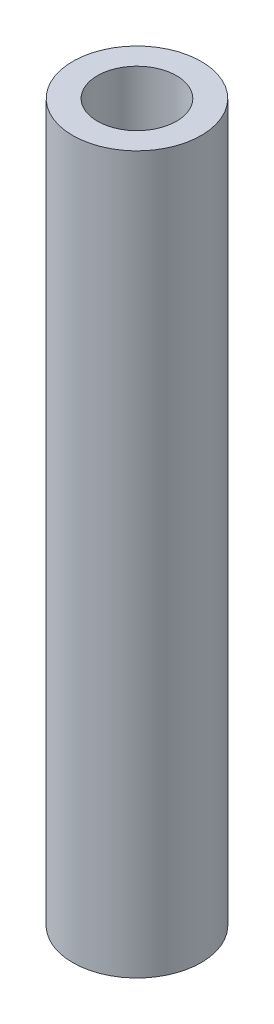
SolidWorks part; units mm, degrees
material "6061-T4 (SS)"
ref_plane "Front Plane" through (0, 0, 0) normal (0, 0, 1) x (1, 0, 0)
ref_plane "Top Plane" through (0, 0, 0) normal (0, 1, 0) x (1, 0, 0)
ref_plane "Right Plane" through (0, 0, 0) normal (1, 0, 0) x (0, 0, -1)
sketch "Sketch1" plane through (0, 0, 0) normal (0, 1, 0) x (1, 0, 0)
  line L0 (0, 0) -> (1.6, 0) construction
  line L1 (1.6, 0) -> (2.6, 0) construction
  circle A0 centre (0, 0) radius 1.6
  circle A1 centre (0, 0) radius 2.6
  dimension "D1" = 3.2
  dimension "D2" = 1
extrude "Boss-Extrude1" add sketch "Sketch1" along normal blind 29
